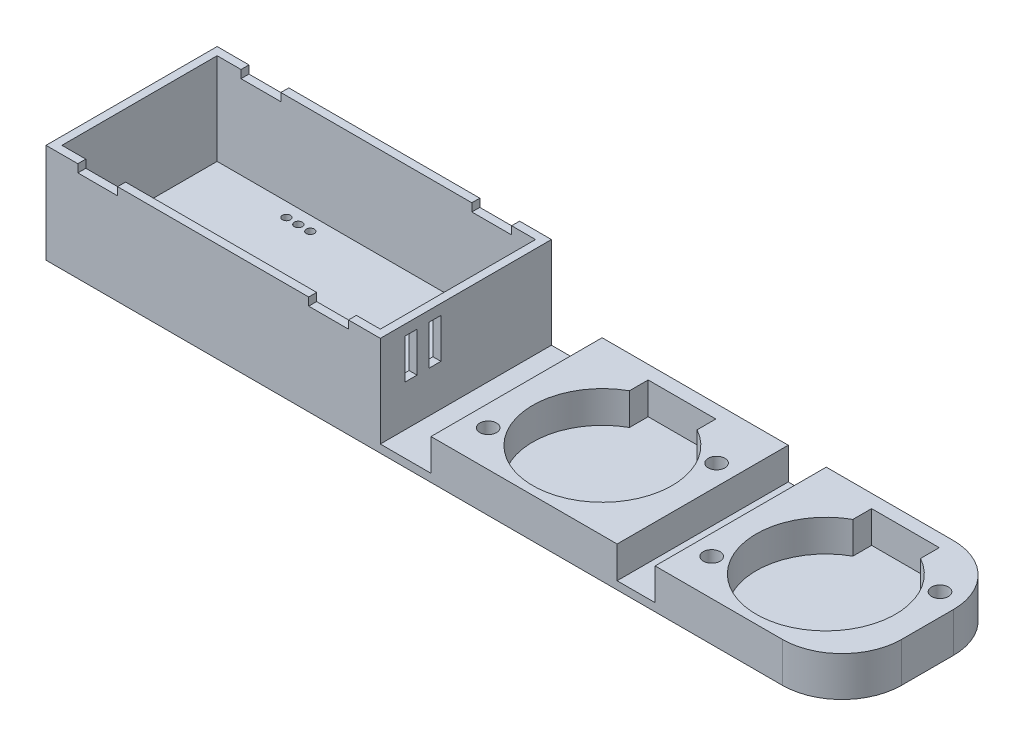
SolidWorks part; units mm, degrees
ref_plane "Front Plane" through (0, 0, 0) normal (0, 0, 1) x (1, 0, 0)
ref_plane "Top Plane" through (0, 0, 0) normal (0, 1, 0) x (1, 0, 0)
ref_plane "Right Plane" through (0, 0, 0) normal (1, 0, 0) x (0, 0, -1)
sketch "Sketch1" plane through (0, 0, 0) normal (0, 1, 0) x (1, 0, 0)
  line L1 (0, 0) -> (200, 0)
  line L2 (0, 0) -> (0, 43)
  line L3 (0, 43) -> (200, 43)
  line L4 (200, 0) -> (200, 43)
  dimension "D1" = 43
  dimension "D2" = 200
extrude "Boss-Extrude1" add sketch "Sketch1" along normal blind 25
sketch "Sketch2" plane through (0, 25, 0) normal (0, 1, 0) x (1, 0, 0)
  line L0 (0, 43) -> (0, 0) construction
  line L1 (2, 2) -> (82, 2)
  line L2 (2, 2) -> (2, 41)
  line L3 (2, 41) -> (82, 41)
  line L4 (82, 2) -> (82, 41)
  line L5 (0, 0) -> (200, 0) construction
  dimension "D1" = 2
  dimension "D2" = 2
  dimension "D3" = 39
  dimension "D4" = 80
extrude "Cut-Extrude1" cut sketch "Sketch2" against normal blind 23
sketch "Sketch3" plane through (0, 0, 0) normal (0, -1, 0) x (1, 0, 0)
  line L1 (11.9146, -28) -> (39.9146, -28)
  line L2 (11.9146, -28) -> (11.9146, -14)
  line L3 (11.9146, -14) -> (39.9146, -14)
  line L4 (39.9146, -28) -> (39.9146, -14)
  dimension "D1" = 14
  dimension "D2" = 28
  dimension "D3" = 14
extrude "Boss-Extrude2" add sketch "Sketch3" along normal blind 8
sketch "Sketch4" plane through (39.9146, 0, 0) normal (1, 0, 0) x (0, 0, -1)
  line L0 (28, -8) -> (28, 0) construction
  line L1 (14, -8) -> (28, -8)
  line L2 (14, -8) -> (14, -6)
  line L3 (14, -6) -> (28, -6)
  line L4 (28, -8) -> (28, -6)
  dimension "D1" = 2
extrude "Boss-Extrude3" add sketch "Sketch4" along normal blind 2.5
sketch "Sketch5" plane through (11.9146, 0, 0) normal (-1, 0, 0) x (0, 0, 1)
  line L0 (-14, -8) -> (-14, 0) construction
  line L1 (-28, -8) -> (-14, -8)
  line L2 (-28, -8) -> (-28, -6)
  line L3 (-28, -6) -> (-14, -6)
  line L4 (-14, -8) -> (-14, -6)
  dimension "D1" = 2
extrude "Boss-Extrude4" add sketch "Sketch5" along normal blind 2.5
sketch "Sketch6" plane through (0, 0, 0) normal (0, -1, 0) x (1, 0, 0)
  line L0 (39.9146, -14) -> (11.9146, -14) construction
  circle A0 centre (25.9146, -37.49) radius 1
  circle A1 centre (28.9146, -37.49) radius 1
  circle A2 centre (22.9146, -37.49) radius 1
  point P4 (25.9146, -14)
  dimension "D1" = 2
  dimension "D2" = 23.49
  dimension "D3" = 2
  dimension "D4" = 2
extrude "Cut-Extrude2" cut sketch "Sketch6" against normal blind 2
sketch "Sketch7" plane through (0, 25, 0) normal (0, 1, 0) x (1, 0, 0)
  line L0 (200, 43) -> (0, 43) construction
  line L1 (82, 2) -> (82, 41) construction
  line L2 (84, 43) -> (200, 43)
  line L3 (84, 43) -> (84, 0)
  line L4 (84, 0) -> (200, 0)
  line L5 (200, 43) -> (200, 0)
  dimension "D1" = 2
extrude "Cut-Extrude3" cut sketch "Sketch7" against normal blind 23
sketch "Sketch8" plane through (0, 2, 0) normal (0, 1, 0) x (1, 0, 0)
  line L0 (184.7695, 39.6728) -> (167.7695, 39.6728)
  line L1 (196.206, 27.1417) -> (192.8687, 25.2149)
  line L2 (192.706, 33.2039) -> (189.3687, 31.2771)
  line L3 (159.6703, 14.1306) -> (156.333, 12.2039)
  line L4 (163.1703, 8.0685) -> (159.833, 6.1417)
  line L5 (184.7695, 34.9698) -> (184.7695, 39.6728)
  line L6 (167.7695, 34.9698) -> (167.7695, 39.6728)
  line L8 (200, 43) -> (153.0463, 43)
  line L9 (200, 43) -> (200, 0)
  line L10 (200, 0) -> (153.0463, 0)
  line L11 (153.0463, 43) -> (153.0463, 0)
  line L14 (200, 0) -> (200, 43) construction
  arc A0 (167.7695, 34.9698) -> (159.6703, 14.1306) centre (176.2695, 19.6728) ccw
  circle A1 centre (194.456, 30.1728) radius 2.1
  circle A2 centre (158.083, 9.1728) radius 2.1
  arc A3 (196.206, 27.1417) -> (192.706, 33.2039) centre (194.456, 30.1728) ccw
  arc A4 (156.333, 12.2039) -> (159.833, 6.1417) centre (158.083, 9.1728) ccw
  arc A5 (189.3687, 31.2771) -> (184.7695, 34.9698) centre (176.2695, 19.6728) ccw
  arc A6 (163.1703, 8.0685) -> (192.8687, 25.2149) centre (176.2695, 19.6728) ccw
  circle A7 centre (176.2695, 19.6728) radius 17.5
  point P2 (176.2695, 19.6728)
  point P5 (191.2256, 19.6728)
  point P6 (191.2256, 19.6728)
  line M14 (84, 0) -> (200, 0)
  line M16 (200, 43) -> (84, 43)
  dimension "D1" = 35
  dimension "D2" = 4.2
  dimension "D3" = 4.2
  dimension "D6" = 7
  dimension "D7" = 7
  dimension "D4" = 21
  dimension "D5" = 21
  dimension "D8" = 17
extrude "Boss-Extrude6" add sketch "Sketch8" along normal blind 8 contours A7 L1 A3 L2 A1 | L11 L9 A6 L4 A4 L3 A0 L6 L0 L5 A5 L2 A3 L1 M14 M16 | A7 L3 A4 L4 A2
sketch "Sketch9" plane through (0, 0, 0) normal (0, 0, 1) x (1, 0, 0)
  line L0 (0, 25) -> (84, 25) construction
  line L1 (8, 25) -> (18, 25)
  line L2 (8, 25) -> (8, 23)
  line L3 (8, 23) -> (18, 23)
  line L4 (18, 25) -> (18, 23)
  line L5 (0, 25) -> (0, 0) construction
  line L6 (66, 25) -> (76, 25)
  line L7 (66, 25) -> (66, 23)
  line L8 (66, 23) -> (76, 23)
  line L9 (76, 25) -> (76, 23)
  line L10 (84, 2) -> (84, 25) construction
  point P12 (8, 24)
  dimension "D1" = 8
  dimension "D2" = 8
  dimension "D3" = 10
  dimension "D4" = 10
  dimension "D5" = 2
  dimension "D6" = 2
extrude "Cut-Extrude4" cut sketch "Sketch9" against normal blind 61
sketch "Sketch10" plane through (0, 2, 0) normal (0, 1, 0) x (1, 0, 0)
  line L0 (128.7036, 39.5937) -> (111.7036, 39.5937)
  line L1 (140.1401, 27.0626) -> (136.8028, 25.1358)
  line L2 (136.6401, 33.1248) -> (133.3028, 31.198)
  line L3 (103.6044, 14.0516) -> (100.2671, 12.1248)
  line L4 (107.1044, 7.9894) -> (103.7671, 6.0626)
  line L5 (128.7036, 34.8908) -> (128.7036, 39.5937)
  line L6 (111.7036, 34.8908) -> (111.7036, 39.5937)
  line L8 (143.5014, 0) -> (96.7322, 0)
  line L9 (143.5014, 0) -> (143.5014, 43)
  line L10 (143.5014, 43) -> (96.7322, 43)
  line L11 (96.7322, 0) -> (96.7322, 43)
  arc A0 (111.7036, 34.8908) -> (103.6044, 14.0516) centre (120.2036, 19.5937) ccw
  circle A1 centre (138.3901, 30.0937) radius 2.1
  circle A2 centre (102.0171, 9.0937) radius 2.1
  arc A3 (140.1401, 27.0626) -> (136.6401, 33.1248) centre (138.3901, 30.0937) ccw
  arc A4 (100.2671, 12.1248) -> (103.7671, 6.0626) centre (102.0171, 9.0937) ccw
  arc A5 (133.3028, 31.198) -> (128.7036, 34.8908) centre (120.2036, 19.5937) ccw
  arc A6 (107.1044, 7.9894) -> (136.8028, 25.1358) centre (120.2036, 19.5937) ccw
  circle A7 centre (120.2036, 19.5937) radius 17.5
  point P2 (120.2036, 19.5937)
  point P5 (126.1958, 19.5106)
  point P6 (126.1958, 19.5106)
  line M19 (153.0463, 43) -> (84, 43)
  line M21 (84, 0) -> (153.0463, 0)
  dimension "D1" = 35
  dimension "D2" = 4.2
  dimension "D3" = 4.2
  dimension "D6" = 7
  dimension "D7" = 7
  dimension "D4" = 21
  dimension "D5" = 21
  dimension "D8" = 17
extrude "Boss-Extrude7" add sketch "Sketch10" along normal blind 8 contours A7 L1 A3 L2 A1 | L11 L9 A6 L4 A4 L3 A0 L6 L0 L5 A5 L2 A3 L1 M19 M21 | A7 L3 A4 L4 A2
sketch "Sketch11" plane through (84, 0, 0) normal (1, 0, 0) x (0, 0, -1)
  line L0 (12.2216, 22.3833) -> (12.2216, 12.3833)
  line L1 (6.2216, 22.3833) -> (9.2216, 22.3833)
  line L2 (6.2216, 22.3833) -> (6.2216, 12.3833)
  line L3 (6.2216, 12.3833) -> (9.2216, 12.3833)
  line L4 (9.2216, 22.3833) -> (9.2216, 12.3833)
  line L5 (12.2216, 22.3833) -> (15.2216, 22.3833)
  line L6 (15.2216, 22.3833) -> (15.2216, 12.3833)
  line L7 (12.2216, 12.3833) -> (15.2216, 12.3833)
  dimension "D1" = 10
  dimension "D2" = 3
  dimension "D3" = 2
extrude "Cut-Extrude5" cut sketch "Sketch11" against normal blind 8
fillet "Fillet1" radius 15 1 edges at (200, 5, 0)
fillet "Fillet2" radius 15 1 edges at (200, 5, -43)
